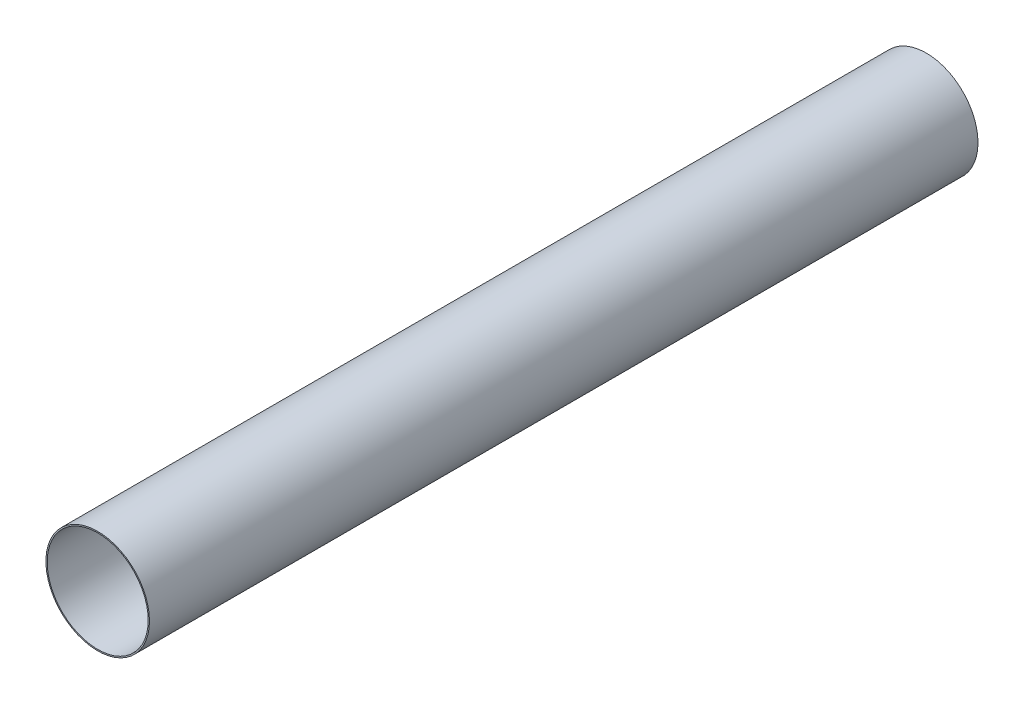
SolidWorks part; units mm, degrees
material "Thornel Mat VMA"
ref_plane "Front Plane" through (0, 0, 0) normal (0, 0, 1) x (1, 0, 0)
ref_plane "Top Plane" through (0, 0, 0) normal (0, 1, 0) x (1, 0, 0)
ref_plane "Right Plane" through (0, 0, 0) normal (1, 0, 0) x (0, 0, -1)
sketch "Sketch1" plane through (0, 0, 0) normal (0, 0, 1) x (1, 0, 0)
  circle A0 centre (0, 0) radius 20.1295
  circle A1 centre (0, 0) radius 20.6375
  dimension "D1" = 0.508
  dimension "D2" = 41.275
extrude "Boss-Extrude1" add sketch "Sketch1" along normal blind 330.2
